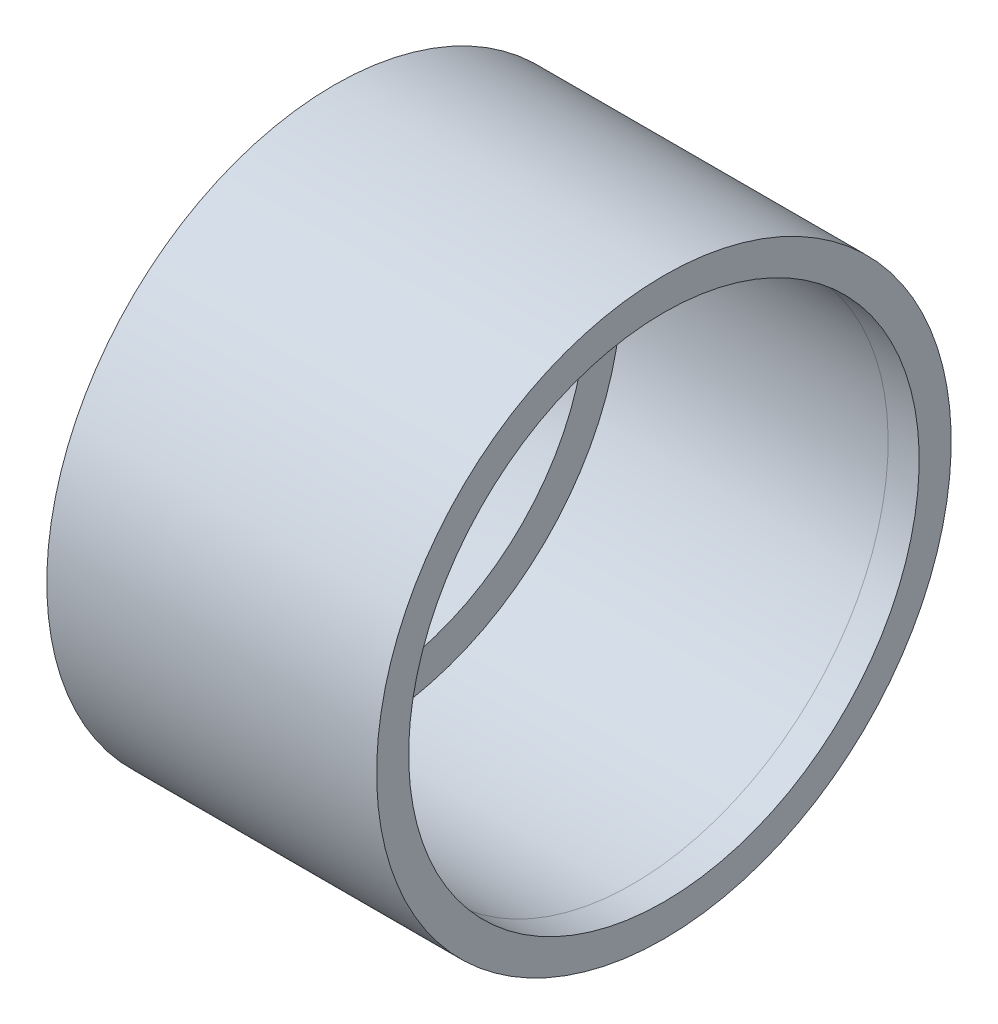
SolidWorks part; units mm, degrees
material "PET"
ref_plane "Front Plane" through (0, 0, 0) normal (0, 0, 1) x (1, 0, 0)
ref_plane "Top Plane" through (0, 0, 0) normal (0, 1, 0) x (1, 0, 0)
ref_plane "Right Plane" through (0, 0, 0) normal (1, 0, 0) x (0, 0, -1)
sketch "Sketch2" plane through (0, 0, 0) normal (0, 0, 1) x (1, 0, 0)
  line L0 (-18.9164, 13.4046) -> (-18.9164, -13.4046) construction
  line L1 (-18.9164, 0) -> (-18.9164, -13.4046)
  line L2 (0, -16.218) -> (0, 16.218) construction
  line L3 (0, -16.218) -> (0, 0) construction
  line L4 (-16.9164, 0) -> (-18.9164, 0)
  line L5 (-18.9164, -13.4046) -> (0, -19.1587) construction
  line L6 (0, -16.218) -> (0, -19.1587) construction
  line L7 (-18.9164, -13.4046) -> (0, 48.782) construction
  line L8 (0, 0) -> (0, 48.782) construction
  line L9 (0, 0) -> (2, 0)
  line L10 (2, 0) -> (2, -18.219)
  line L11 (2, -18.219) -> (0, -18.219)
  line L12 (-18.9164, -13.4046) -> (-18.9164, -18.219)
  line L13 (0, -18.219) -> (-18.9164, -18.219)
  line L14 (-16.9164, 0) -> (-16.9164, -16.219)
  line L16 (0, -16.218) -> (0, 0)
  line L17 (-16.9164, -16.219) -> (0, -16.219)
  line L18 (0, -16.219) -> (0, -16.218)
  arc A0 (-18.9164, -13.4046) -> (0, -16.218) centre (0, 48.782) ccw construction
  arc A1 (-18.9164, -13.4046) -> (0, -16.218) centre (0, 48.782) ccw construction
  dimension "D1" = 2
  dimension "D2" = 2
  dimension "D3" = 2
  dimension "D4" = 0.001
revolve "Revolve1" add sketch "Sketch2" angle 360 about L4
sketch "Sketch5" plane through (0, 0, 0) normal (0, 0, 1) x (1, 0, 0)
  line L0 (0, 0) -> (0, 48.782) construction
  line L1 (-18.9164, 0) -> (-18.9164, -13.4046) construction
  line L2 (-18.9164, 0) -> (-18.9164, -13.4046)
  line L3 (-18.9164, -13.4046) -> (-18.9164, -18.219) construction
  line L4 (-18.9164, -13.4046) -> (-18.9164, -13.4056)
  line L5 (2, 0) -> (2, -18.219) construction
  line L6 (2, 0) -> (2, -16.1882)
  line L7 (-18.9164, 0) -> (2, 0)
  arc A0 (-18.9164, -13.4056) -> (2, -16.1882) centre (0, 48.781) ccw
  arc A1 (-18.9164, -13.4046) -> (0, -16.218) centre (0, 48.782) ccw construction
revolve "Cut-Revolve2" cut sketch "Sketch5" angle 360 about L7
